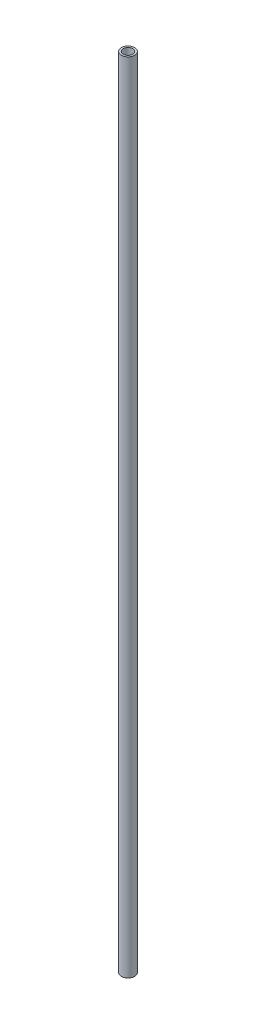
SolidWorks part; units mm, degrees
material "AISI Type 316L stainless steel"
ref_plane "Front Plane" through (0, 0, 0) normal (0, 0, 1) x (1, 0, 0)
ref_plane "Top Plane" through (0, 0, 0) normal (0, 1, 0) x (1, 0, 0)
ref_plane "Right Plane" through (0, 0, 0) normal (1, 0, 0) x (0, 0, -1)
sketch "Sketch1" plane through (0, 0, 0) normal (0, 1, 0) x (1, 0, 0)
  circle A0 centre (0, 0) radius 3.175
  circle A1 centre (0, 0) radius 2.286
  dimension "D1" = 6.35
  dimension "D2" = 4.572
extrude "Boss-Extrude1" add sketch "Sketch1" along normal blind 381
